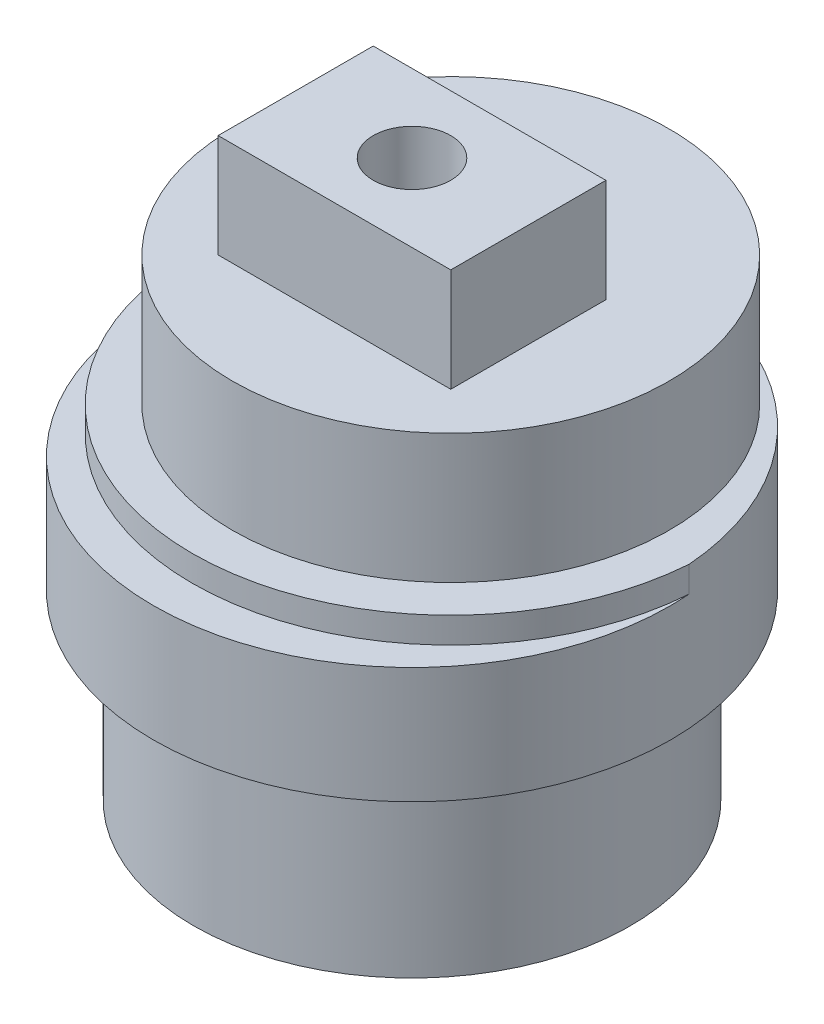
SolidWorks part; units mm, degrees
ref_plane "Front Plane" through (0, 0, 0) normal (0, 0, 1) x (1, 0, 0)
ref_plane "Top Plane" through (0, 0, 0) normal (0, 1, 0) x (1, 0, 0)
ref_plane "Right Plane" through (0, 0, 0) normal (1, 0, 0) x (0, 0, -1)
sketch "Sketch1" plane through (0, 0, 0) normal (0, 1, 0) x (1, 0, 0)
  circle A0 centre (0, 0) radius 8.45
  dimension "D1" = 16.9
extrude "Boss-Extrude1" add sketch "Sketch1" along normal blind 7
sketch "Sketch2" plane through (0, 7, 0) normal (0, 1, 0) x (1, 0, 0)
  circle A0 centre (0, 0) radius 10
  dimension "D1" = 20
extrude "Boss-Extrude2" add sketch "Sketch2" along normal blind 4.5
sketch "Sketch3" plane through (0, 11.5, 0) normal (0, 1, 0) x (1, 0, 0)
  circle A0 centre (0, 1.5) radius 8.45
  dimension "D1" = 16.9
  dimension "D2" = 1.5
extrude "Boss-Extrude3" add sketch "Sketch3" along normal blind 6
sketch "Sketch4" plane through (0, 11.5, 0) normal (0, 1, 0) x (1, 0, 0)
  circle A0 centre (0, 1.5) radius 8.45 construction
  circle A1 centre (0, 1.5) radius 8.45
  circle A2 centre (0, 0) radius 10 construction
  arc A3 (0, -10) -> (-9.9718, 0.75) centre (0, 0) ccw
  arc A4 (-9.9718, 0.75) -> (9.9718, 0.75) centre (0, 1.5) ccw
  arc A5 (9.9718, 0.75) -> (0, -10) centre (0, 0) ccw
  circle M1 centre (0, 1.5) radius 8.45
  circle M2 centre (0, 0) radius 10
  dimension "D1" = 20
extrude "Boss-Extrude4" add sketch "Sketch4" along normal blind 1 contours A4 M2 M1
sketch "Sketch5" plane through (0, 17.5, 0) normal (0, 1, 0) x (1, 0, 0)
  line L1 (-4.5, -3) -> (4.5, -3)
  line L2 (-4.5, -3) -> (-4.5, 3)
  line L3 (-4.5, 3) -> (4.5, 3)
  line L4 (4.5, -3) -> (4.5, 3)
  line L5 (-4.5, -3) -> (4.5, 3) construction
  line L6 (-4.5, 3) -> (4.5, -3) construction
  point P2 (0, 0)
  dimension "D3" = 9
  dimension "D4" = 6
extrude "Boss-Extrude5" add sketch "Sketch5" along normal blind 4
sketch "Sketch6" plane through (0, 21.5, 0) normal (0, 1, 0) x (1, 0, 0)
  circle A0 centre (0, 0) radius 1.5
  dimension "D1" = 3
extrude "Cut-Extrude1" cut sketch "Sketch6" against normal blind 8
sketch "Sketch7" plane through (0, 0, 0) normal (0, -1, 0) x (-1, 0, 0)
  circle A0 centre (0, -5.5) radius 1.5
  circle A1 centre (-5.5, 0) radius 1.5
  circle A2 centre (0, 5.5) radius 1.5
  circle A3 centre (5.5, 0) radius 1.5
  point P12 (0, 0)
  dimension "D3" = 3
  dimension "D1" = 5.5
  dimension "D2" = 4
extrude "Cut-Extrude2" [suppressed] cut sketch "Sketch7" against normal blind 8
sketch "Sketch8" plane through (0, 0, 0) normal (0, -1, 0) x (1, 0, 0)
  arc A0 (1.9433, 2.9259) -> (1.4435, 3.2021) centre (0, 0) ccw
  arc A1 (-2.4201, 2.5457) -> (-2.8006, 2.1199) centre (0, 0) ccw
  arc A2 (3.4992, 0.3049) -> (3.4036, 0.8679) centre (0, 0) ccw
  arc A3 (2.4201, -2.5457) -> (2.8006, -2.1199) centre (0, 0) ccw
  arc A4 (-1.0759, 3.3436) -> (-1.6035, 3.1251) centre (0, 0) ccw
  arc A5 (-3.0204, -1.793) -> (-2.6899, -2.2587) centre (0, 0) ccw
  arc A6 (0.4814, 3.4793) -> (-0.0888, 3.5113) centre (0, 0) ccw
  arc A7 (3.0204, 1.793) -> (2.6899, 2.2587) centre (0, 0) ccw
  arc A8 (3.285, -1.2435) -> (3.4431, -0.6948) centre (0, 0) ccw
  arc A9 (-3.285, 1.2435) -> (-3.4431, 0.6948) centre (0, 0) ccw
  arc A10 (1.0759, -3.3436) -> (1.6035, -3.1251) centre (0, 0) ccw
  arc A11 (-1.9433, -2.9259) -> (-1.4435, -3.2021) centre (0, 0) ccw
  arc A12 (-0.4814, -3.4793) -> (0.0888, -3.5113) centre (0, 0) ccw
  arc A13 (-3.4992, -0.3049) -> (-3.4036, -0.8679) centre (0, 0) ccw
  spline S0 degree 3 poles (-2.6899, -2.2587) (-2.6998, -2.278) (-2.7192, -2.3185) (-2.7467, -2.3829) (-2.7734, -2.4537) (-2.7988, -2.5314) (-2.8225, -2.6162) (-2.8438, -2.7079) (-2.8627, -2.8065) (-2.877, -2.9191) (-2.8909, -3.0073) (-2.8865, -3.0684) (-2.8815, -3.0926) (-2.874, -3.1162) (-2.8635, -3.1386) (-2.8488, -3.1646) (-2.8257, -3.1852) (-2.7982, -3.1969) (-2.7748, -3.2048) (-2.7506, -3.2097) (-2.7259, -3.2119) (-2.6647, -3.2094) (-2.5786, -3.1858) (-2.4684, -3.1589) (-2.3725, -3.1291) (-2.2837, -3.0977) (-2.2021, -3.0646) (-2.1277, -3.0307) (-2.0604, -2.9963) (-1.9994, -2.9617) (-1.9614, -2.9379) (-1.9433, -2.9259) knots 0.027203 0.027203 0.027203 0.027203 0.059318 0.093556 0.130845 0.171187 0.214581 0.261026 0.310525 0.363075 0.429245 0.441417 0.453589 0.465761 0.477933 0.490104 0.509896 0.522067 0.534239 0.546411 0.558583 0.570755 0.636925 0.689475 0.738974 0.785419 0.828813 0.869155 0.906444 0.940682 0.972797 0.972797 0.972797 0.972797 weights 1 1 1 1 1 1 1 1 1 1 1 1 1 1 1 1 1 1 1 1 1 1 1 1 1 1 1 1 1 1 1 1
  spline S1 degree 3 poles (-1.6035, 3.1251) (-1.6202, 3.139) (-1.6552, 3.1669) (-1.7119, 3.2081) (-1.775, 3.2498) (-1.8451, 3.2919) (-1.9225, 3.3339) (-2.0072, 3.3751) (-2.0992, 3.4154) (-2.2057, 3.4545) (-2.2886, 3.4876) (-2.3492, 3.4969) (-2.3739, 3.4975) (-2.3985, 3.4953) (-2.4227, 3.4901) (-2.4514, 3.4815) (-2.4765, 3.4637) (-2.4941, 3.4395) (-2.507, 3.4184) (-2.5172, 3.3958) (-2.5248, 3.3723) (-2.536, 3.312) (-2.5321, 3.2229) (-2.5304, 3.1094) (-2.5227, 3.0093) (-2.5119, 2.9157) (-2.4978, 2.8289) (-2.4812, 2.7487) (-2.4627, 2.6754) (-2.4425, 2.6083) (-2.4278, 2.566) (-2.4201, 2.5457) knots 0.027203 0.027203 0.027203 0.027203 0.059318 0.093556 0.130845 0.171187 0.214581 0.261026 0.310525 0.363075 0.429245 0.441417 0.453589 0.465761 0.477933 0.490104 0.509896 0.522067 0.534239 0.546411 0.558583 0.570755 0.636925 0.689475 0.738974 0.785419 0.828813 0.869155 0.906444 0.940682 0.972797 0.972797 0.972797 0.972797 weights 1 1 1 1 1 1 1 1 1 1 1 1 1 1 1 1 1 1 1 1 1 1 1 1 1 1 1 1 1 1 1 1
  spline S2 degree 3 poles (2.6899, 2.2587) (2.6998, 2.278) (2.7192, 2.3185) (2.7467, 2.3829) (2.7734, 2.4537) (2.7988, 2.5314) (2.8225, 2.6162) (2.8438, 2.7079) (2.8627, 2.8065) (2.877, 2.9191) (2.8909, 3.0073) (2.8865, 3.0684) (2.8815, 3.0926) (2.874, 3.1162) (2.8635, 3.1386) (2.8488, 3.1646) (2.8257, 3.1852) (2.7982, 3.1969) (2.7748, 3.2048) (2.7506, 3.2097) (2.7259, 3.2119) (2.6647, 3.2094) (2.5786, 3.1858) (2.4684, 3.1589) (2.3725, 3.1291) (2.2837, 3.0977) (2.2021, 3.0646) (2.1277, 3.0307) (2.0604, 2.9963) (1.9994, 2.9617) (1.9614, 2.9379) (1.9433, 2.9259) knots 0.027203 0.027203 0.027203 0.027203 0.059318 0.093556 0.130845 0.171187 0.214581 0.261026 0.310525 0.363075 0.429245 0.441417 0.453589 0.465761 0.477933 0.490104 0.509896 0.522067 0.534239 0.546411 0.558583 0.570755 0.636925 0.689475 0.738974 0.785419 0.828813 0.869155 0.906444 0.940682 0.972797 0.972797 0.972797 0.972797 weights 1 1 1 1 1 1 1 1 1 1 1 1 1 1 1 1 1 1 1 1 1 1 1 1 1 1 1 1 1 1 1 1
  spline S3 degree 3 poles (3.4036, 0.8679) (3.4208, 0.881) (3.4559, 0.909) (3.5086, 0.9551) (3.5633, 1.0074) (3.62, 1.0664) (3.6781, 1.1324) (3.7371, 1.2058) (3.7969, 1.2865) (3.8587, 1.3817) (3.9094, 1.4551) (3.9319, 1.5121) (3.938, 1.5361) (3.9414, 1.5606) (3.9417, 1.5853) (3.9397, 1.6152) (3.9279, 1.6437) (3.9082, 1.6662) (3.8905, 1.6835) (3.8708, 1.6984) (3.8495, 1.7111) (3.7933, 1.7354) (3.7055, 1.7515) (3.5945, 1.7751) (3.4952, 1.7899) (3.4016, 1.8001) (3.3137, 1.8057) (3.232, 1.8073) (3.1564, 1.8056) (3.0865, 1.8009) (3.0419, 1.7959) (3.0204, 1.793) knots 0.027203 0.027203 0.027203 0.027203 0.059318 0.093556 0.130845 0.171187 0.214581 0.261026 0.310525 0.363075 0.429245 0.441417 0.453589 0.465761 0.477933 0.490104 0.509896 0.522067 0.534239 0.546411 0.558583 0.570755 0.636925 0.689475 0.738974 0.785419 0.828813 0.869155 0.906444 0.940682 0.972797 0.972797 0.972797 0.972797 weights 1 1 1 1 1 1 1 1 1 1 1 1 1 1 1 1 1 1 1 1 1 1 1 1 1 1 1 1 1 1 1 1
  spline S4 degree 3 poles (2.8006, -2.1199) (2.8217, -2.1252) (2.8654, -2.1351) (2.9343, -2.1476) (3.0093, -2.1578) (3.0907, -2.1653) (3.1786, -2.1696) (3.2728, -2.1699) (3.3732, -2.1664) (3.4861, -2.1553) (3.5751, -2.1492) (3.6338, -2.1313) (3.6563, -2.1211) (3.6776, -2.1085) (3.6971, -2.0933) (3.7192, -2.0731) (3.7341, -2.0461) (3.7394, -2.0167) (3.7419, -1.9921) (3.7413, -1.9674) (3.7379, -1.9429) (3.7219, -1.8837) (3.6797, -1.8051) (3.629, -1.7036) (3.5786, -1.6167) (3.5282, -1.5371) (3.4778, -1.465) (3.4281, -1.4) (3.3796, -1.342) (3.3324, -1.2903) (3.3007, -1.2585) (3.285, -1.2435) knots 0.027203 0.027203 0.027203 0.027203 0.059318 0.093556 0.130845 0.171187 0.214581 0.261026 0.310525 0.363075 0.429245 0.441417 0.453589 0.465761 0.477933 0.490104 0.509896 0.522067 0.534239 0.546411 0.558583 0.570755 0.636925 0.689475 0.738974 0.785419 0.828813 0.869155 0.906444 0.940682 0.972797 0.972797 0.972797 0.972797 weights 1 1 1 1 1 1 1 1 1 1 1 1 1 1 1 1 1 1 1 1 1 1 1 1 1 1 1 1 1 1 1 1
  spline S5 degree 3 poles (-2.8006, 2.1199) (-2.8217, 2.1252) (-2.8654, 2.1351) (-2.9343, 2.1476) (-3.0093, 2.1578) (-3.0907, 2.1653) (-3.1786, 2.1696) (-3.2728, 2.1699) (-3.3732, 2.1664) (-3.4861, 2.1553) (-3.5751, 2.1492) (-3.6338, 2.1313) (-3.6563, 2.1211) (-3.6776, 2.1085) (-3.6971, 2.0933) (-3.7192, 2.0731) (-3.7341, 2.0461) (-3.7394, 2.0167) (-3.7419, 1.9921) (-3.7413, 1.9674) (-3.7379, 1.9429) (-3.7219, 1.8837) (-3.6797, 1.8051) (-3.629, 1.7036) (-3.5786, 1.6167) (-3.5282, 1.5371) (-3.4778, 1.465) (-3.4281, 1.4) (-3.3796, 1.342) (-3.3324, 1.2903) (-3.3007, 1.2585) (-3.285, 1.2435) knots 0.027203 0.027203 0.027203 0.027203 0.059318 0.093556 0.130845 0.171187 0.214581 0.261026 0.310525 0.363075 0.429245 0.441417 0.453589 0.465761 0.477933 0.490104 0.509896 0.522067 0.534239 0.546411 0.558583 0.570755 0.636925 0.689475 0.738974 0.785419 0.828813 0.869155 0.906444 0.940682 0.972797 0.972797 0.972797 0.972797 weights 1 1 1 1 1 1 1 1 1 1 1 1 1 1 1 1 1 1 1 1 1 1 1 1 1 1 1 1 1 1 1 1
  spline S6 degree 3 poles (1.4435, 3.2021) (1.444, 3.2238) (1.444, 3.2687) (1.4408, 3.3387) (1.4341, 3.414) (1.4233, 3.4951) (1.4079, 3.5817) (1.3873, 3.6736) (1.3615, 3.7707) (1.3256, 3.8783) (1.2998, 3.9638) (1.2693, 4.0169) (1.2543, 4.0366) (1.2373, 4.0546) (1.2182, 4.0702) (1.1936, 4.0872) (1.1639, 4.0958) (1.134, 4.0944) (1.1095, 4.0914) (1.0855, 4.0852) (1.0624, 4.0765) (1.0083, 4.0478) (0.941, 3.9891) (0.8533, 3.9171) (0.7798, 3.8486) (0.7135, 3.7818) (0.6543, 3.7166) (0.6021, 3.6537) (0.5563, 3.5935) (0.5164, 3.5359) (0.4925, 3.498) (0.4814, 3.4793) knots 0.027203 0.027203 0.027203 0.027203 0.059318 0.093556 0.130845 0.171187 0.214581 0.261026 0.310525 0.363075 0.429245 0.441417 0.453589 0.465761 0.477933 0.490104 0.509896 0.522067 0.534239 0.546411 0.558583 0.570755 0.636925 0.689475 0.738974 0.785419 0.828813 0.869155 0.906444 0.940682 0.972797 0.972797 0.972797 0.972797 weights 1 1 1 1 1 1 1 1 1 1 1 1 1 1 1 1 1 1 1 1 1 1 1 1 1 1 1 1 1 1 1 1
  spline S7 degree 3 poles (-1.4435, -3.2021) (-1.444, -3.2238) (-1.444, -3.2687) (-1.4408, -3.3387) (-1.4341, -3.414) (-1.4233, -3.4951) (-1.4079, -3.5817) (-1.3873, -3.6736) (-1.3615, -3.7707) (-1.3256, -3.8783) (-1.2998, -3.9638) (-1.2693, -4.0169) (-1.2543, -4.0366) (-1.2373, -4.0546) (-1.2182, -4.0702) (-1.1936, -4.0872) (-1.1639, -4.0958) (-1.134, -4.0944) (-1.1095, -4.0914) (-1.0855, -4.0852) (-1.0624, -4.0765) (-1.0083, -4.0478) (-0.941, -3.9891) (-0.8533, -3.9171) (-0.7798, -3.8486) (-0.7135, -3.7818) (-0.6543, -3.7166) (-0.6021, -3.6537) (-0.5563, -3.5935) (-0.5164, -3.5359) (-0.4925, -3.498) (-0.4814, -3.4793) knots 0.027203 0.027203 0.027203 0.027203 0.059318 0.093556 0.130845 0.171187 0.214581 0.261026 0.310525 0.363075 0.429245 0.441417 0.453589 0.465761 0.477933 0.490104 0.509896 0.522067 0.534239 0.546411 0.558583 0.570755 0.636925 0.689475 0.738974 0.785419 0.828813 0.869155 0.906444 0.940682 0.972797 0.972797 0.972797 0.972797 weights 1 1 1 1 1 1 1 1 1 1 1 1 1 1 1 1 1 1 1 1 1 1 1 1 1 1 1 1 1 1 1 1
  spline S8 degree 3 poles (-3.4036, -0.8679) (-3.4208, -0.881) (-3.4559, -0.909) (-3.5086, -0.9551) (-3.5633, -1.0074) (-3.62, -1.0664) (-3.6781, -1.1324) (-3.7371, -1.2058) (-3.7969, -1.2865) (-3.8587, -1.3817) (-3.9094, -1.4551) (-3.9319, -1.5121) (-3.938, -1.5361) (-3.9414, -1.5606) (-3.9417, -1.5853) (-3.9397, -1.6152) (-3.9279, -1.6437) (-3.9082, -1.6662) (-3.8905, -1.6835) (-3.8708, -1.6984) (-3.8495, -1.7111) (-3.7933, -1.7354) (-3.7055, -1.7515) (-3.5945, -1.7751) (-3.4952, -1.7899) (-3.4016, -1.8001) (-3.3137, -1.8057) (-3.232, -1.8073) (-3.1564, -1.8056) (-3.0865, -1.8009) (-3.0419, -1.7959) (-3.0204, -1.793) knots 0.027203 0.027203 0.027203 0.027203 0.059318 0.093556 0.130845 0.171187 0.214581 0.261026 0.310525 0.363075 0.429245 0.441417 0.453589 0.465761 0.477933 0.490104 0.509896 0.522067 0.534239 0.546411 0.558583 0.570755 0.636925 0.689475 0.738974 0.785419 0.828813 0.869155 0.906444 0.940682 0.972797 0.972797 0.972797 0.972797 weights 1 1 1 1 1 1 1 1 1 1 1 1 1 1 1 1 1 1 1 1 1 1 1 1 1 1 1 1 1 1 1 1
  spline S9 degree 3 poles (3.4431, -0.6948) (3.4643, -0.6905) (3.508, -0.6804) (3.5756, -0.6618) (3.6475, -0.6385) (3.7242, -0.6099) (3.8052, -0.5756) (3.8902, -0.535) (3.9791, -0.4883) (4.0761, -0.4293) (4.1536, -0.3852) (4.1987, -0.3436) (4.2145, -0.3246) (4.2282, -0.304) (4.2392, -0.2819) (4.2504, -0.2541) (4.2521, -0.2233) (4.2441, -0.1945) (4.2357, -0.1713) (4.2244, -0.1493) (4.2107, -0.1286) (4.1706, -0.0823) (4.0985, -0.0298) (4.0087, 0.0397) (3.9256, 0.0961) (3.8457, 0.1459) (3.769, 0.1891) (3.6961, 0.2261) (3.6272, 0.2573) (3.5622, 0.2834) (3.5199, 0.2982) (3.4992, 0.3049) knots 0.027203 0.027203 0.027203 0.027203 0.059318 0.093556 0.130845 0.171187 0.214581 0.261026 0.310525 0.363075 0.429245 0.441417 0.453589 0.465761 0.477933 0.490104 0.509896 0.522067 0.534239 0.546411 0.558583 0.570755 0.636925 0.689475 0.738974 0.785419 0.828813 0.869155 0.906444 0.940682 0.972797 0.972797 0.972797 0.972797 weights 1 1 1 1 1 1 1 1 1 1 1 1 1 1 1 1 1 1 1 1 1 1 1 1 1 1 1 1 1 1 1 1
  spline S10 degree 3 poles (-0.0888, 3.5113) (-0.0977, 3.5311) (-0.1172, 3.5715) (-0.1505, 3.6332) (-0.1892, 3.6981) (-0.2341, 3.7665) (-0.2856, 3.8379) (-0.344, 3.9117) (-0.4094, 3.988) (-0.4885, 4.0694) (-0.5487, 4.1352) (-0.5993, 4.1698) (-0.6213, 4.1811) (-0.6444, 4.1899) (-0.6685, 4.1957) (-0.698, 4.2003) (-0.7284, 4.1952) (-0.7548, 4.181) (-0.7755, 4.1676) (-0.7945, 4.1517) (-0.8116, 4.1338) (-0.8478, 4.0844) (-0.883, 4.0024) (-0.9307, 3.8994) (-0.9672, 3.8058) (-0.998, 3.7168) (-1.023, 3.6325) (-1.0429, 3.5531) (-1.058, 3.479) (-1.0689, 3.4098) (-1.074, 3.3652) (-1.0759, 3.3436) knots 0.027203 0.027203 0.027203 0.027203 0.059318 0.093556 0.130845 0.171187 0.214581 0.261026 0.310525 0.363075 0.429245 0.441417 0.453589 0.465761 0.477933 0.490104 0.509896 0.522067 0.534239 0.546411 0.558583 0.570755 0.636925 0.689475 0.738974 0.785419 0.828813 0.869155 0.906444 0.940682 0.972797 0.972797 0.972797 0.972797 weights 1 1 1 1 1 1 1 1 1 1 1 1 1 1 1 1 1 1 1 1 1 1 1 1 1 1 1 1 1 1 1 1
  spline S11 degree 3 poles (1.6035, -3.1251) (1.6202, -3.139) (1.6552, -3.1669) (1.7119, -3.2081) (1.775, -3.2498) (1.8451, -3.2919) (1.9225, -3.3339) (2.0072, -3.3751) (2.0992, -3.4154) (2.2057, -3.4545) (2.2886, -3.4876) (2.3492, -3.4969) (2.3739, -3.4975) (2.3985, -3.4953) (2.4227, -3.4901) (2.4514, -3.4815) (2.4765, -3.4637) (2.4941, -3.4395) (2.507, -3.4184) (2.5172, -3.3958) (2.5248, -3.3723) (2.536, -3.312) (2.5321, -3.2229) (2.5304, -3.1094) (2.5227, -3.0093) (2.5119, -2.9157) (2.4978, -2.8289) (2.4812, -2.7487) (2.4627, -2.6754) (2.4425, -2.6083) (2.4278, -2.566) (2.4201, -2.5457) knots 0.027203 0.027203 0.027203 0.027203 0.059318 0.093556 0.130845 0.171187 0.214581 0.261026 0.310525 0.363075 0.429245 0.441417 0.453589 0.465761 0.477933 0.490104 0.509896 0.522067 0.534239 0.546411 0.558583 0.570755 0.636925 0.689475 0.738974 0.785419 0.828813 0.869155 0.906444 0.940682 0.972797 0.972797 0.972797 0.972797 weights 1 1 1 1 1 1 1 1 1 1 1 1 1 1 1 1 1 1 1 1 1 1 1 1 1 1 1 1 1 1 1 1
  spline S12 degree 3 poles (-3.4431, 0.6948) (-3.4643, 0.6905) (-3.508, 0.6804) (-3.5756, 0.6618) (-3.6475, 0.6385) (-3.7242, 0.6099) (-3.8052, 0.5756) (-3.8902, 0.535) (-3.9791, 0.4883) (-4.0761, 0.4293) (-4.1536, 0.3852) (-4.1987, 0.3436) (-4.2145, 0.3246) (-4.2282, 0.304) (-4.2392, 0.2819) (-4.2504, 0.2541) (-4.2521, 0.2233) (-4.2441, 0.1945) (-4.2357, 0.1713) (-4.2244, 0.1493) (-4.2107, 0.1286) (-4.1706, 0.0823) (-4.0985, 0.0298) (-4.0087, -0.0397) (-3.9256, -0.0961) (-3.8457, -0.1459) (-3.769, -0.1891) (-3.6961, -0.2261) (-3.6272, -0.2573) (-3.5622, -0.2834) (-3.5199, -0.2982) (-3.4992, -0.3049) knots 0.027203 0.027203 0.027203 0.027203 0.059318 0.093556 0.130845 0.171187 0.214581 0.261026 0.310525 0.363075 0.429245 0.441417 0.453589 0.465761 0.477933 0.490104 0.509896 0.522067 0.534239 0.546411 0.558583 0.570755 0.636925 0.689475 0.738974 0.785419 0.828813 0.869155 0.906444 0.940682 0.972797 0.972797 0.972797 0.972797 weights 1 1 1 1 1 1 1 1 1 1 1 1 1 1 1 1 1 1 1 1 1 1 1 1 1 1 1 1 1 1 1 1
  spline S13 degree 3 poles (0.0888, -3.5113) (0.0977, -3.5311) (0.1172, -3.5715) (0.1505, -3.6332) (0.1892, -3.6981) (0.2341, -3.7665) (0.2856, -3.8379) (0.344, -3.9117) (0.4094, -3.988) (0.4885, -4.0694) (0.5487, -4.1352) (0.5993, -4.1698) (0.6213, -4.1811) (0.6444, -4.1899) (0.6685, -4.1957) (0.698, -4.2003) (0.7284, -4.1952) (0.7548, -4.181) (0.7755, -4.1676) (0.7945, -4.1517) (0.8116, -4.1338) (0.8478, -4.0844) (0.883, -4.0024) (0.9307, -3.8994) (0.9672, -3.8058) (0.998, -3.7168) (1.023, -3.6325) (1.0429, -3.5531) (1.058, -3.479) (1.0689, -3.4098) (1.074, -3.3652) (1.0759, -3.3436) knots 0.027203 0.027203 0.027203 0.027203 0.059318 0.093556 0.130845 0.171187 0.214581 0.261026 0.310525 0.363075 0.429245 0.441417 0.453589 0.465761 0.477933 0.490104 0.509896 0.522067 0.534239 0.546411 0.558583 0.570755 0.636925 0.689475 0.738974 0.785419 0.828813 0.869155 0.906444 0.940682 0.972797 0.972797 0.972797 0.972797 weights 1 1 1 1 1 1 1 1 1 1 1 1 1 1 1 1 1 1 1 1 1 1 1 1 1 1 1 1 1 1 1 1
extrude "Cut-Extrude3" [suppressed] cut sketch "Sketch8" against normal blind 16
sketch "Sketch9" plane through (0, 0, 0) normal (0, -1, 0) x (-1, 0, 0)
  line L0 (1.3191, -1.15) -> (-1.3191, -1.15)
  arc A0 (1.3191, -1.15) -> (-1.3191, -1.15) centre (0, 0) ccw
  dimension "D1" = 3.5
  dimension "D2" = 1.15
extrude "Cut-Extrude4" cut sketch "Sketch9" against normal blind 10
chamfer "Chamfer1" distance 1 angle 45 2 edges at (0, 0, 1.15) (0, 0, -1.75)
